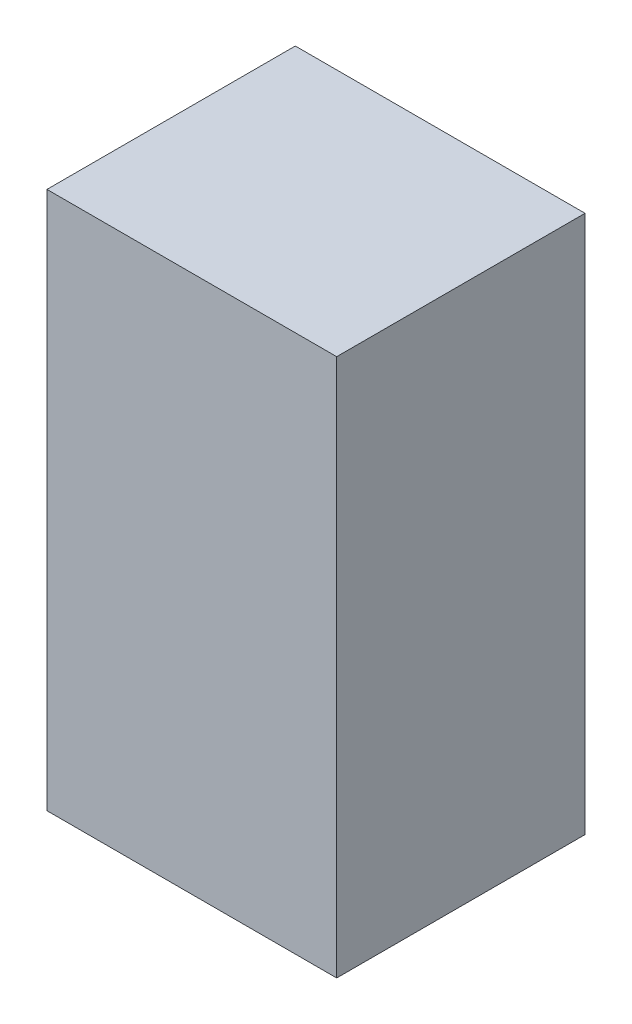
SolidWorks part; units mm, degrees
ref_plane "Front Plane" through (0, 0, 0) normal (0, 0, 1) x (1, 0, 0)
ref_plane "Top Plane" through (0, 0, 0) normal (0, 1, 0) x (1, 0, 0)
ref_plane "Right Plane" through (0, 0, 0) normal (1, 0, 0) x (0, 0, -1)
sketch "Sketch1" plane through (0, 0, 0) normal (0, 0, 1) x (1, 0, 0)
  line L1 (-427.8087, 379.8957) -> (-357.8087, 379.8957)
  line L2 (-427.8087, 379.8957) -> (-427.8087, 249.8957)
  line L3 (-427.8087, 249.8957) -> (-357.8087, 249.8957)
  line L4 (-357.8087, 379.8957) -> (-357.8087, 249.8957)
  dimension "D1" = 70
  dimension "D2" = 130
extrude "Boss-Extrude1" add sketch "Sketch1" along normal blind 60
